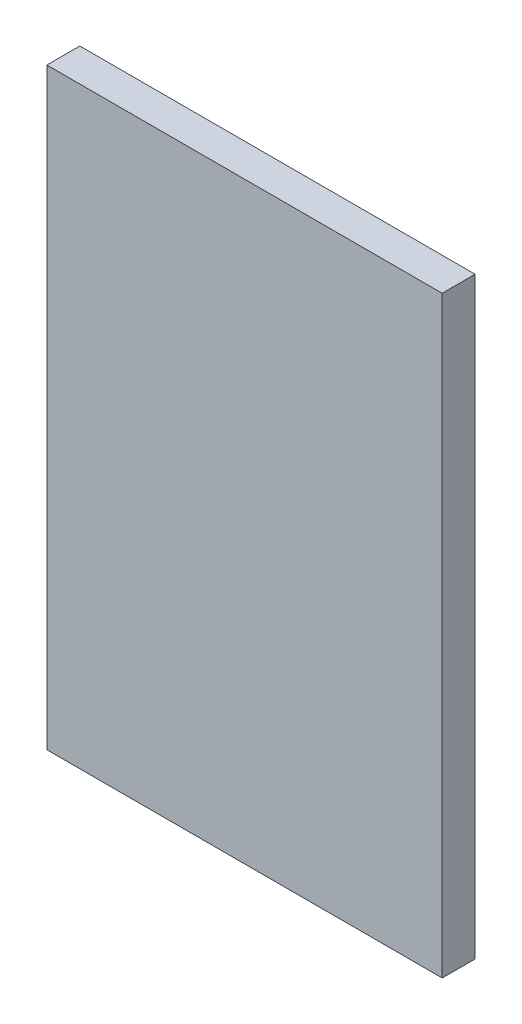
SolidWorks part; units mm, degrees
ref_plane "Alzado" through (0, 0, 0) normal (0, 0, 1) x (1, 0, 0)
ref_plane "Planta" through (0, 0, 0) normal (0, 1, 0) x (1, 0, 0)
ref_plane "Vista lateral" through (0, 0, 0) normal (1, 0, 0) x (0, 0, -1)
sketch "Croquis1" plane through (0, 0, 0) normal (0, 0, 1) x (1, 0, 0)
  line L1 (-30, -45) -> (30, -45)
  line L2 (-30, -45) -> (-30, 45)
  line L3 (-30, 45) -> (30, 45)
  line L4 (30, -45) -> (30, 45)
  line L5 (-30, -45) -> (30, 45) construction
  line L6 (-30, 45) -> (30, -45) construction
  point P0 (0, 0)
  dimension "D1" = 90
  dimension "D2" = 60
extrude "Saliente-Extruir1" add sketch "Croquis1" along normal blind 5
